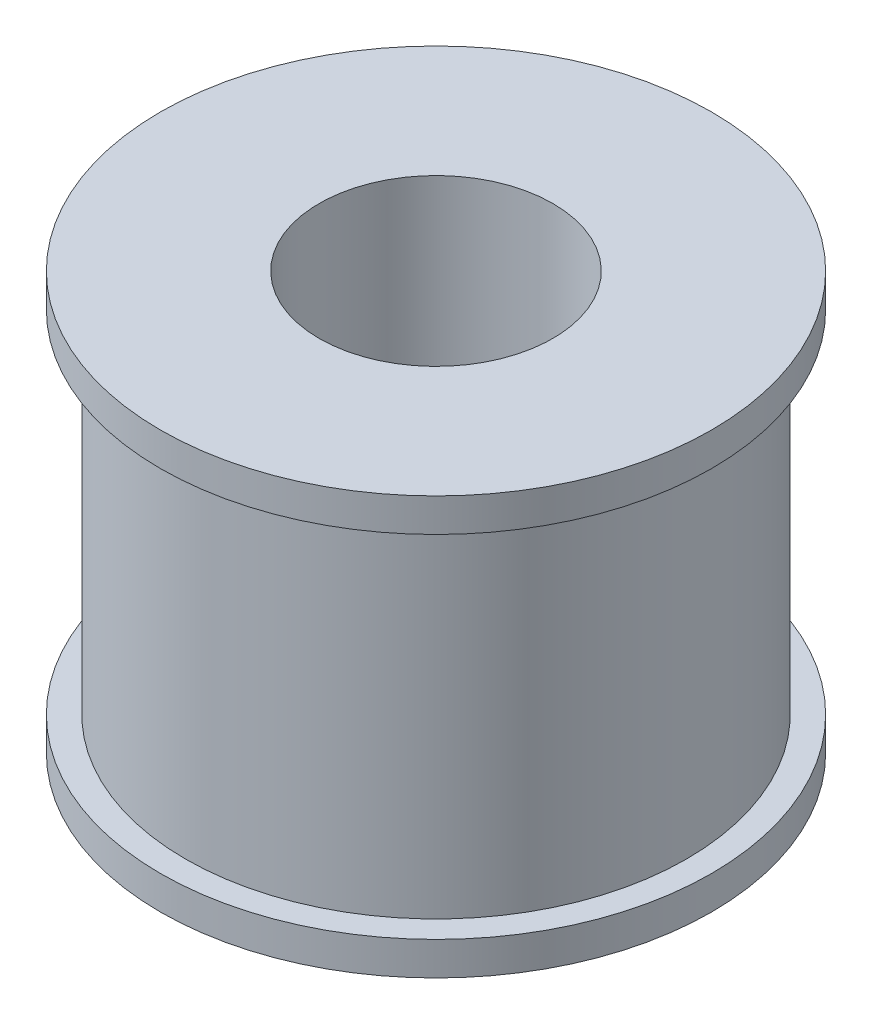
SolidWorks part; units mm, degrees
ref_plane "Alzado" through (0, 0, 0) normal (0, 0, 1) x (1, 0, 0)
ref_plane "Planta" through (0, 0, 0) normal (0, 1, 0) x (1, 0, 0)
ref_plane "Vista lateral" through (0, 0, 0) normal (1, 0, 0) x (0, 0, -1)
sketch "Croquis1" plane through (0, 0, 0) normal (0, 1, 0) x (1, 0, 0)
  circle A0 centre (0, 0) radius 3
  circle A1 centre (0, 0) radius 15
  dimension "D1" = 6
  dimension "D2" = 30
extrude "Saliente-Extruir1" add sketch "Croquis1" along normal blind 25
sketch "Croquis2" plane through (0, 0, 0) normal (0, -1, 0) x (1, 0, 0)
  circle A0 centre (0, 0) radius 3
  circle A1 centre (0, 0) radius 16.5
  dimension "D1" = 33
extrude "Saliente-Extruir2" add sketch "Croquis2" against normal blind 2
sketch "Croquis3" plane through (0, 25, 0) normal (0, 1, 0) x (1, 0, 0)
  circle A0 centre (0, 0) radius 3
  circle A1 centre (0, 0) radius 16.5
  dimension "D1" = 33
extrude "Saliente-Extruir3" add sketch "Croquis3" against normal blind 2
sketch "Croquis4" plane through (0, 0, 0) normal (0, 0, 1) x (1, 0, 0)
  line L2 (-16.5, 0) -> (16.5, 0) construction
  circle A0 centre (0, 5) radius 1.625
  dimension "D1" = 3.25
  dimension "D2" = 5
extrude "Cortar-Extruir1" cut sketch "Croquis4" against normal up to next
sketch "Croquis5" plane through (0, 25, 0) normal (0, 1, 0) x (1, 0, 0)
  circle A0 centre (0, 0) radius 7
  dimension "D1" = 14
extrude "Cortar-Extruir2" cut sketch "Croquis5" against normal blind 16
